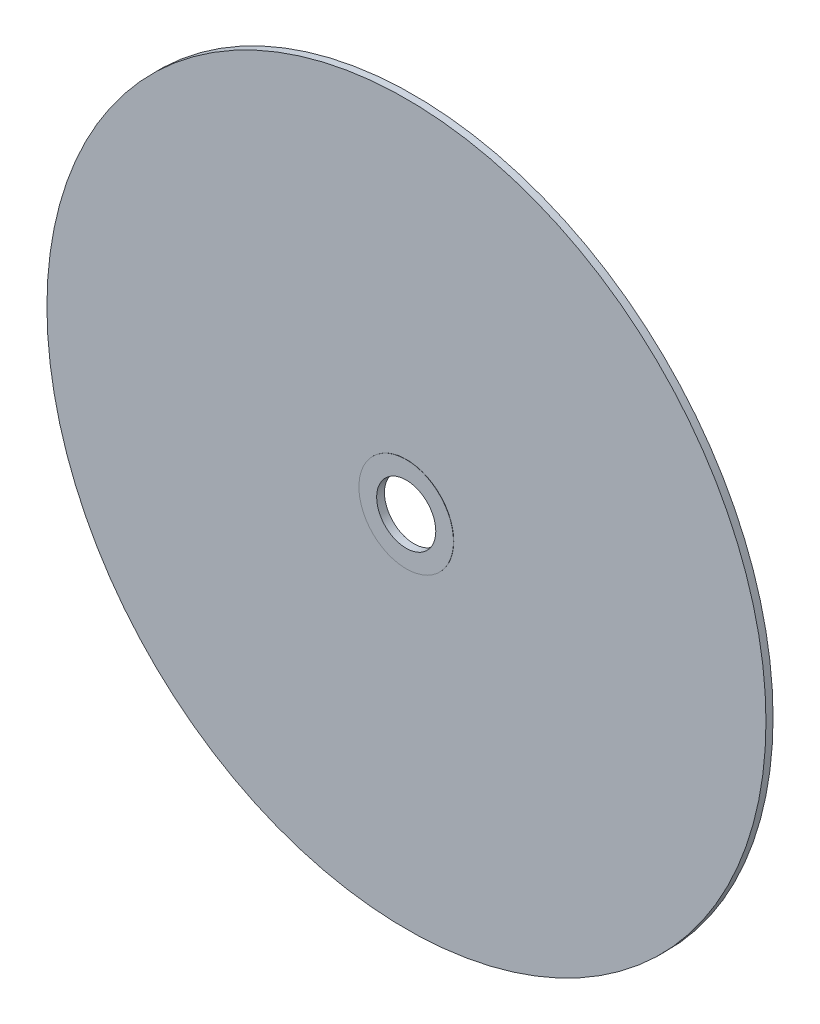
SolidWorks part; units mm, degrees
ref_plane "Front Plane" through (0, 0, 0) normal (0, 0, 1) x (1, 0, 0)
ref_plane "Top Plane" through (0, 0, 0) normal (0, 1, 0) x (1, 0, 0)
ref_plane "Right Plane" through (0, 0, 0) normal (1, 0, 0) x (0, 0, -1)
sketch "Sketch1" plane through (0, 0, 0) normal (0, 0, 1) x (1, 0, 0)
  circle A0 centre (0, 0) radius 152
  dimension "D1" = 304
extrude "Boss-Extrude1" add sketch "Sketch1" along normal blind 3
sketch "Sketch2" plane through (0, 0, 3) normal (0, 0, 1) x (1, 0, 0)
  circle A0 centre (0, 0) radius 12.5
  dimension "D1" = 25
extrude "Cut-Extrude1" cut sketch "Sketch2" against normal blind 3
sketch "Sketch3" plane through (0, 0, 3) normal (0, 0, 1) x (1, 0, 0)
  circle A0 centre (0, 0) radius 20
  dimension "D1" = 40
extrude "Boss-Extrude2" add sketch "Sketch3" along normal blind 0.1 and the other way blind 3.2
sketch "Sketch4" plane through (0, 0, -0.2) normal (0, 0, -1) x (-1, 0, 0)
  circle A0 centre (0, 0) radius 12.5
  dimension "D1" = 25
extrude "Cut-Extrude2" cut sketch "Sketch4" against normal blind 50.1
